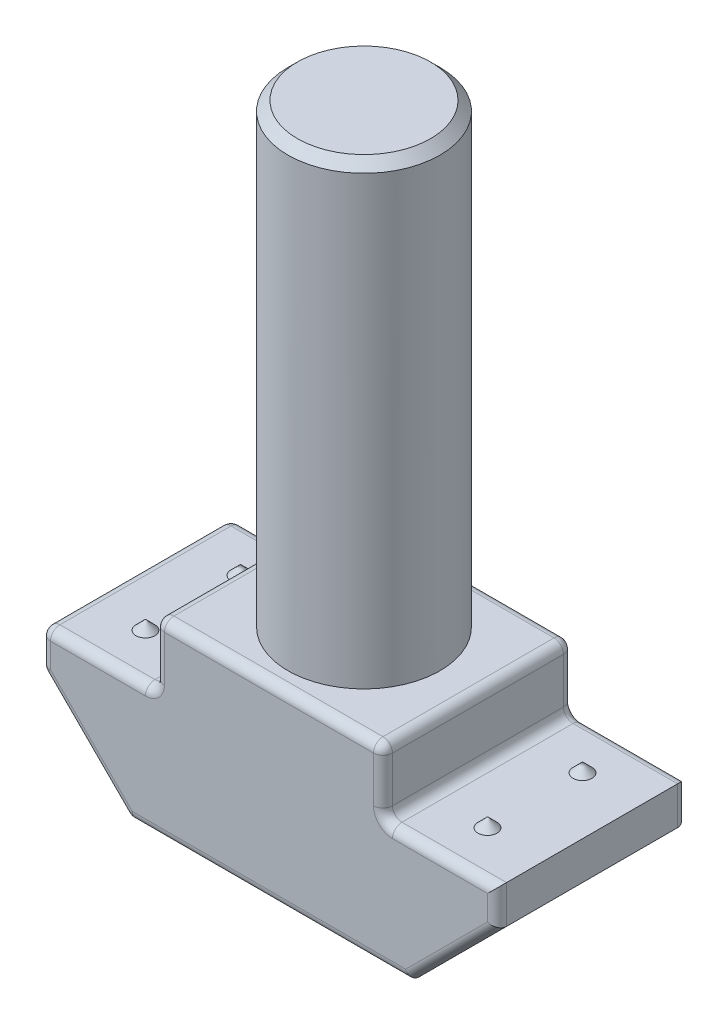
SolidWorks part; units mm, degrees
material "Acciaio inossidabile al cromo"
ref_plane "Piano frontale" through (0, 0, 0) normal (0, 0, 1) x (1, 0, 0)
ref_plane "Piano superiore" through (0, 0, 0) normal (0, 1, 0) x (1, 0, 0)
ref_plane "Piano destro" through (0, 0, 0) normal (1, 0, 0) x (0, 0, -1)
sketch "Schizzo1" plane through (0, 0, 0) normal (0, 0, 1) x (1, 0, 0)
  line L10 (3.7, 0) -> (-3.7, 0)
  line L11 (-3.7, 0) -> (-6, 2.3)
  line L12 (-6, 2.3) -> (-6, 3.3)
  line L13 (-6, 3.3) -> (-3, 3.3)
  line L14 (-3, 3.3) -> (-3, 5)
  line L15 (-3, 5) -> (3, 5)
  line L20 (0, 0) -> (0, 5) construction
  line L21 (0, -3.19) -> (0, 3.19) construction
  line L22 (6, 3.3) -> (3, 3.3)
  line L23 (6, 2.3) -> (6, 3.3)
  line L24 (3.7, 0) -> (6, 2.3)
  line L25 (3, 3.3) -> (3, 5)
  dimension "D1" = 3
  dimension "D2" = 3.3
  dimension "D3" = 1
  dimension "D4" = 45
  dimension "D5" = 6
  dimension "D6" = 5
extrude "Estrusione-Estrusione1" add sketch "Schizzo1" along normal blind 5
ref_plane "Piano1" through (0, 0, 2.5) normal (0, 0, 1) x (1, 0, 0)
fillet "Raccordo1" radius 0.25 27 edges at (3, 3.3, 2.5) (3, 5, 2.5) (-4.5, 3.3, 5) (0, 5, 5) (3, 4.15, 5) (4.5, 3.3, 5) (6, 2.8, 5) (4.85, 1.15, 5) (0, 0, 5) (-3, 5, 2.5) (-3, 4.15, 5) (-3, 3.3, 2.5) (-6, 3.3, 2.5) (-6, 2.8, 5) (-6, 2.3, 2.5) (-4.85, 1.15, 5) (-3.7, 0, 2.5) (0, 0, 0) (4.85, 1.15, 0) (6, 2.8, 0) (4.5, 3.3, 0) (3, 4.15, 0) (0, 5, 0) (-3, 4.15, 0) (-4.5, 3.3, 0) (-6, 2.8, 0) (-4.85, 1.15, 0)
sketch "Schizzo7" plane through (0, 5, 0) normal (0, 1, 0) x (1, 0, 0)
  line L0 (-2.75, -2.5) -> (2.75, -2.5) construction
  line L1 (-2.75, -0.25) -> (-2.75, -4.75) construction
  line L2 (2.75, -4.75) -> (2.75, -0.25) construction
  circle A0 centre (0, -2.5) radius 2
  dimension "D1" = 4
extrude "Estrusione-Estrusione3" add sketch "Schizzo7" along normal blind 12
cosmetic thread "Filettatura cosmetica1" parameters "D2"=3.22
chamfer "Smusso1" distance 0.25 angle 45 1 edges at (0, 17, 4.5)
ref_plane "Piano4" through (0, 0, 1.25) normal (0, 0, 1) x (1, 0, 0)
sketch "Schizzo8" plane through (0, 0, 1.25) normal (0, 0, 1) x (1, 0, 0)
  line L0 (-4.5, 3.3) -> (-4.5, 3.55)
  line L1 (-5.75, 3.3) -> (-3.25, 3.3) construction
  line L2 (-4.5, 3.55) -> (-4.75, 3.3)
  line L3 (-4.75, 3.3) -> (-4.5, 3.3)
  line L4 (-4.5, 3.3) -> (-4.5, 4.2152) construction
  dimension "D1" = 0.25
  dimension "D2" = 45
revolve "Rivoluzione2" add sketch "Schizzo8" angle 360 about L4
mirror "Specchia3" about plane through (0, 0, 0) normal (1, 0, 0) of "Rivoluzione2"
mirror "Specchia4" about plane through (0, 0, 2.5) normal (0, 0, 1) of "Specchia3", "Rivoluzione2"
